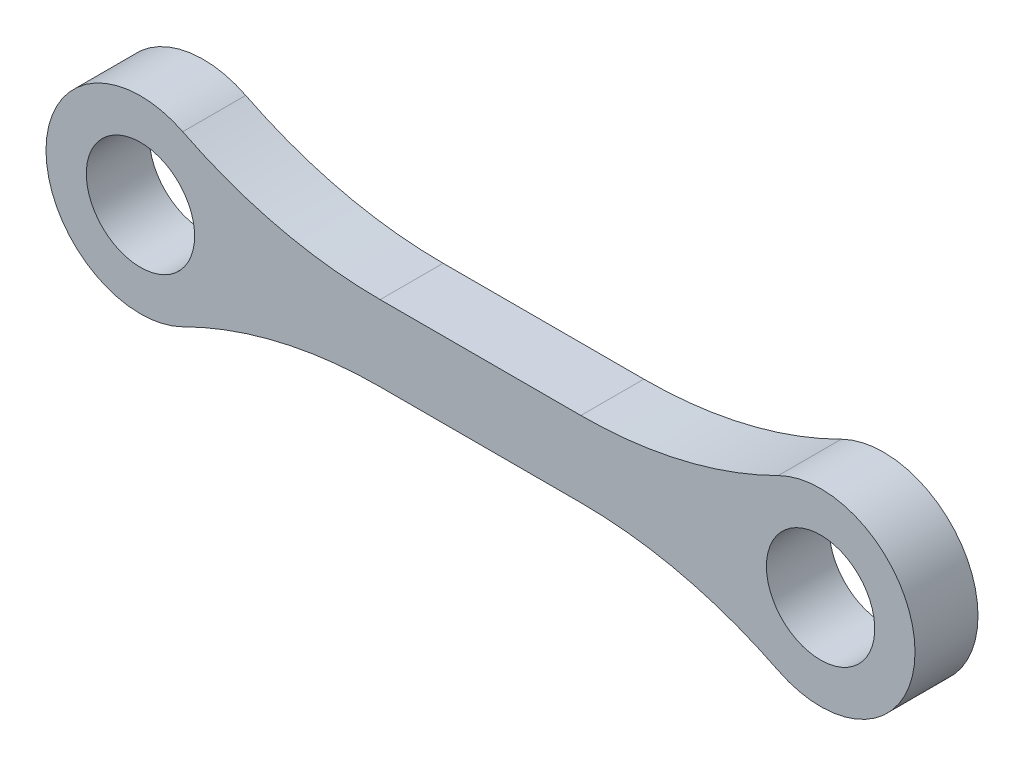
SolidWorks part; units mm, degrees
ref_plane "Alzado" through (0, 0, 0) normal (0, 0, 1) x (1, 0, 0)
ref_plane "Planta" through (0, 0, 0) normal (0, 1, 0) x (1, 0, 0)
ref_plane "Vista lateral" through (0, 0, 0) normal (1, 0, 0) x (0, 0, -1)
sketch "Croquis1" plane through (0, 0, 0) normal (0, 0, 1) x (1, 0, 0)
  line L0 (73.4599, 0) -> (-63.4244, 0) construction
  line L1 (0, 41.0096) -> (0, -50.8266) construction
  line L3 (-7.9671, 3) -> (7.9671, 3)
  line L5 (-7.9671, -3) -> (7.9671, -3)
  circle A0 centre (-27, 0) radius 4.3
  arc A1 (-23.6413, 6.7059) -> (-23.6413, -6.7059) centre (-27, 0) ccw
  arc A2 (23.6413, 6.7059) -> (23.6413, -6.7059) centre (27, 0) cw
  circle A3 centre (27, 0) radius 4.3
  arc A4 (7.9671, -3) -> (23.6413, -6.7059) centre (7.9671, -38) cw
  arc A5 (7.9671, 3) -> (23.6413, 6.7059) centre (7.9671, 38) ccw
  arc A6 (-23.6413, -6.7059) -> (-7.9671, -3) centre (-7.9671, -38) cw
  arc A7 (-23.6413, 6.7059) -> (-7.9671, 3) centre (-7.9671, 38) ccw
  point P11 (0, 0)
  dimension "D2" = 8.6
  dimension "D3" = 15
  dimension "D6" = 35
  dimension "D1" = 27
  dimension "D4" = 6
  dimension "D5" = 3
extrude "Saliente-Extruir1" add sketch "Croquis1" along normal blind 5
